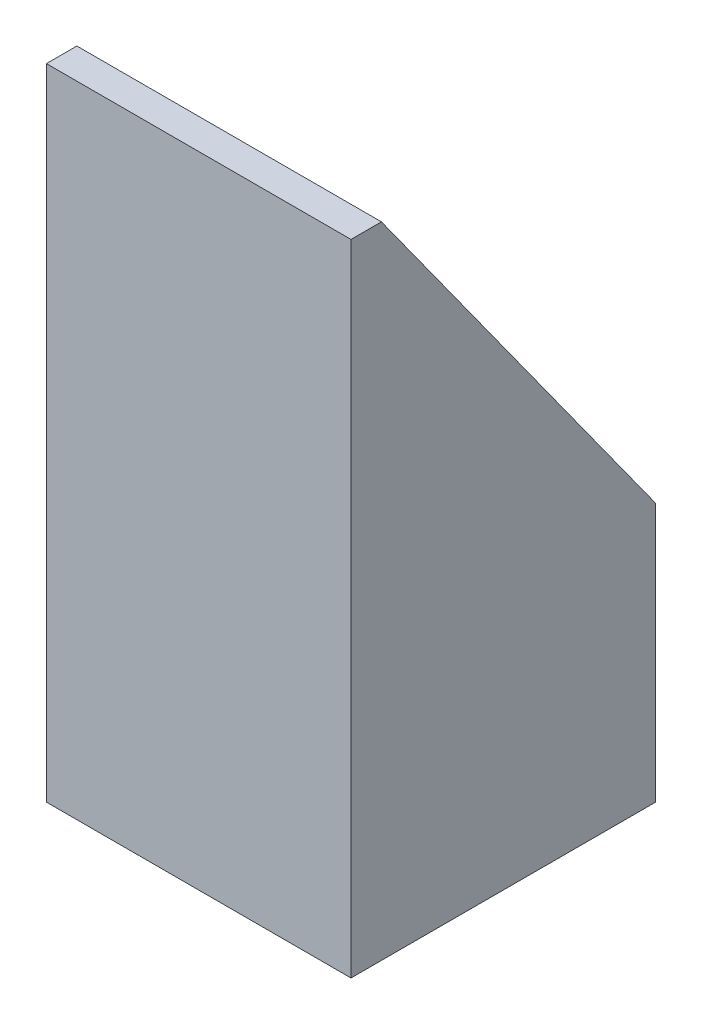
SolidWorks part; units mm, degrees
ref_plane "Płaszczyzna przednia" through (0, 0, 0) normal (0, 0, 1) x (1, 0, 0)
ref_plane "Płaszczyzna górna" through (0, 0, 0) normal (0, 1, 0) x (1, 0, 0)
ref_plane "Płaszczyzna prawa" through (0, 0, 0) normal (1, 0, 0) x (0, 0, -1)
sketch "Szkic1" plane through (0, 0, 0) normal (0, 1, 0) x (1, 0, 0)
  line L0 (2, -2) -> (2, -18)
  line L1 (0, 0) -> (20, 0)
  line L2 (0, 0) -> (0, -20)
  line L3 (0, -20) -> (20, -20)
  line L4 (20, 0) -> (20, -20)
  line L5 (2, -18) -> (18, -18)
  line L6 (18, -2) -> (18, -18)
  line L7 (2, -2) -> (18, -2)
  dimension "D1" = 20
  dimension "D2" = 20
  dimension "D3" = 2
extrude "Dodanie-wyciągnięcie1" add sketch "Szkic1" along normal blind 40
sketch "Szkic2" plane through (20, 0, 0) normal (1, 0, 0) x (0, 0, -1)
  line L0 (-18, 40) -> (0, 15)
  line L1 (-20, 40) -> (0, 40) construction
  line L2 (0, 40) -> (0, 0) construction
  line L3 (0, 15) -> (0, 40)
  line L4 (0, 40) -> (-18, 40)
  line L5 (-20, 0) -> (0, 0) construction
  dimension "D1" = 2
  dimension "D2" = 15
extrude "Wytnij-wyciągnięcie1" cut sketch "Szkic2" against normal through all both and the other way through all
sketch "Szkic3" plane through (0, 0, 0) normal (0, -1, 0) x (1, 0, 0)
  line L1 (20, 20) -> (0, 20)
  line L2 (20, 20) -> (20, 0)
  line L3 (20, 0) -> (0, 0)
  line L4 (0, 20) -> (0, 0)
extrude "Dodanie-wyciągnięcie2" add sketch "Szkic3" along normal blind 2
sketch "Szkic4" plane through (0, -2, 0) normal (0, -1, 0) x (1, 0, 0)
  line L0 (0, 0) -> (20, 0) construction
  line L1 (0, 20) -> (0, 0) construction
  line L2 (20, 20) -> (0, 20) construction
  circle A0 centre (10, 14) radius 2
  circle A1 centre (10, 6) radius 2
  dimension "D1" = 4
  dimension "D2" = 4
  dimension "D3" = 6
  dimension "D4" = 10
  dimension "D5" = 10
  dimension "D6" = 6
extrude "Wytnij-wyciągnięcie2" cut sketch "Szkic4" against normal blind 2
